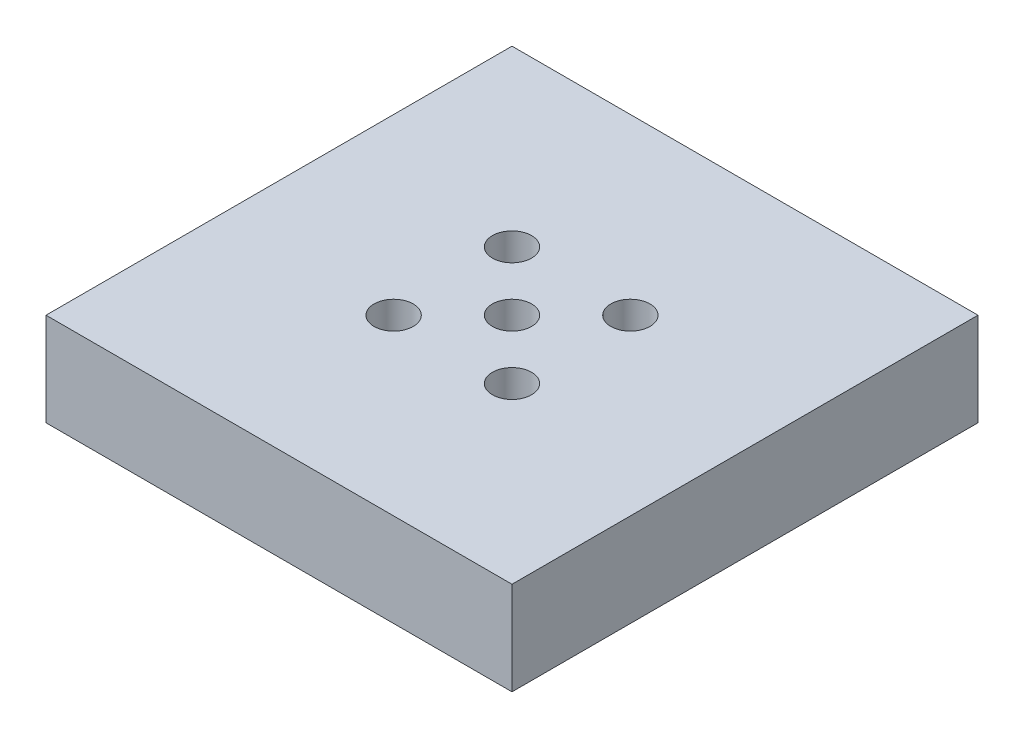
SolidWorks part; units mm, degrees
ref_plane "Front Plane" through (0, 0, 0) normal (0, 0, 1) x (1, 0, 0)
ref_plane "Top Plane" through (0, 0, 0) normal (0, 1, 0) x (1, 0, 0)
ref_plane "Right Plane" through (0, 0, 0) normal (1, 0, 0) x (0, 0, -1)
sketch "Sketch2" plane through (0, 0, 0) normal (0, 1, 0) x (1, 0, 0)
  line L1 (-25, 25) -> (25, 25)
  line L2 (-25, 25) -> (-25, -25)
  line L3 (-25, -25) -> (25, -25)
  line L4 (25, 25) -> (25, -25)
  line L5 (-25, 25) -> (25, -25) construction
  line L6 (-25, -25) -> (25, 25) construction
  point P0 (0, 0)
  dimension "D1" = 50
  dimension "D2" = 50
extrude "Boss-Extrude1" add sketch "Sketch2" along normal blind 10
sketch "Sketch4" plane through (0, 10, 0) normal (0, 1, 0) x (1, 0, 0)
  circle A0 centre (0, 0) radius 2.1
  circle A1 centre (6.35, 6.35) radius 2.1
  circle A2 centre (-6.35, 6.35) radius 2.1
  circle A3 centre (-6.35, -6.35) radius 2.1
  circle A4 centre (6.35, -6.35) radius 2.1
  point P11 (0, 0)
  point P12 (0, 0)
  point P13 (-9.1258, -9.9762)
  dimension "D1" = 6.35
  dimension "D9" = 4.2
  dimension "D10" = 4.2
  dimension "D11" = 4.2
  dimension "D12" = 4.2
  dimension "D2" = 6.35
  dimension "D3" = 6.35
  dimension "D4" = 6.35
  dimension "D5" = 6.35
  dimension "D6" = 6.35
  dimension "D7" = 6.35
  dimension "D8" = 6.35
extrude "Cut-Extrude1" cut sketch "Sketch4" against normal blind 4.57
sketch "Sketch5" plane through (0, 0, 0) normal (0, -1, 0) x (1, 0, 0)
  line L1 (-10, -10) -> (10, -10)
  line L2 (-10, -10) -> (-10, 10)
  line L3 (-10, 10) -> (10, 10)
  line L4 (10, -10) -> (10, 10)
  line L5 (-10, -10) -> (10, 10) construction
  line L6 (-10, 10) -> (10, -10) construction
  point P0 (0, 0)
  dimension "D1" = 20
  dimension "D2" = 20
extrude "Cut-Extrude2" cut sketch "Sketch5" against normal up to surface (5.43 mm away) up to face at (-6.35, 5.43, 8.45)
